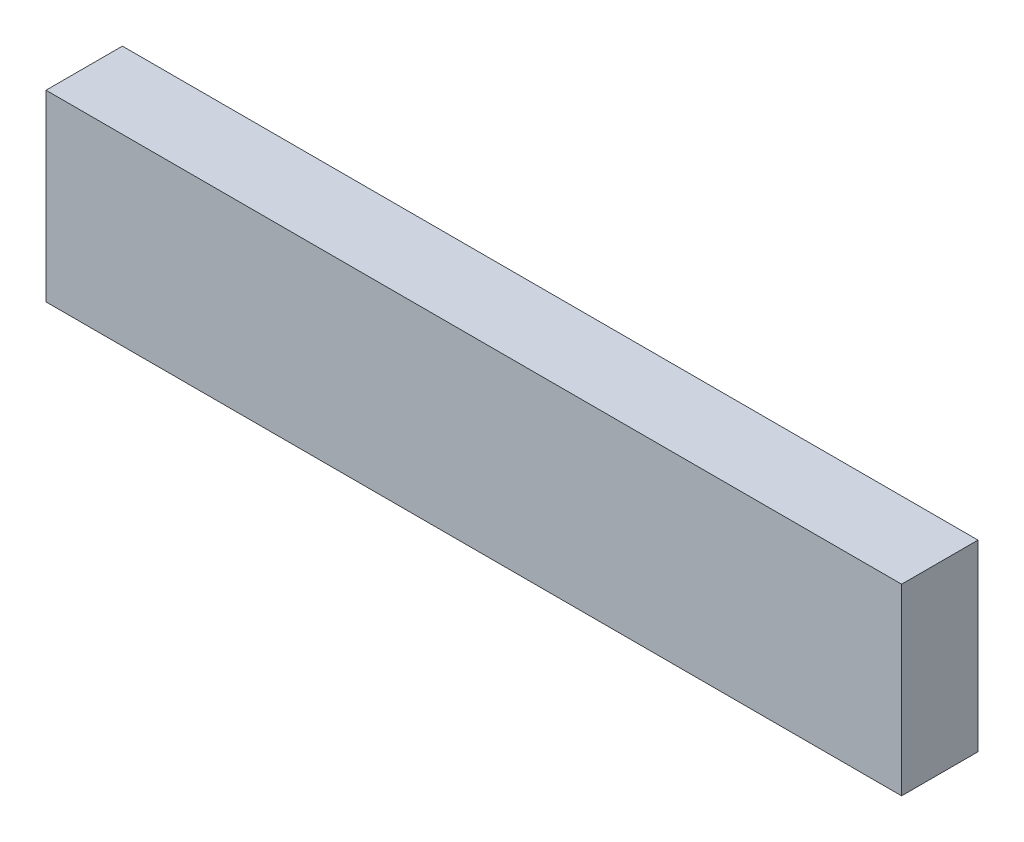
SolidWorks part; units mm, degrees
ref_plane "前基準面" through (0, 0, 0) normal (0, 0, 1) x (1, 0, 0)
ref_plane "上基準面" through (0, 0, 0) normal (0, 1, 0) x (1, 0, 0)
ref_plane "右基準面" through (0, 0, 0) normal (1, 0, 0) x (0, 0, -1)
sketch "草圖1" plane through (0, 0, 0) normal (0, 0, 1) x (1, 0, 0)
  line L1 (-37.246, 15.4103) -> (18.754, 15.4103)
  line L2 (-37.246, 15.4103) -> (-37.246, 3.4103)
  line L3 (-37.246, 3.4103) -> (18.754, 3.4103)
  line L4 (18.754, 15.4103) -> (18.754, 3.4103)
  dimension "D1" = 56
  dimension "D2" = 12
extrude "填料-伸長1" add sketch "草圖1" along normal blind 5
